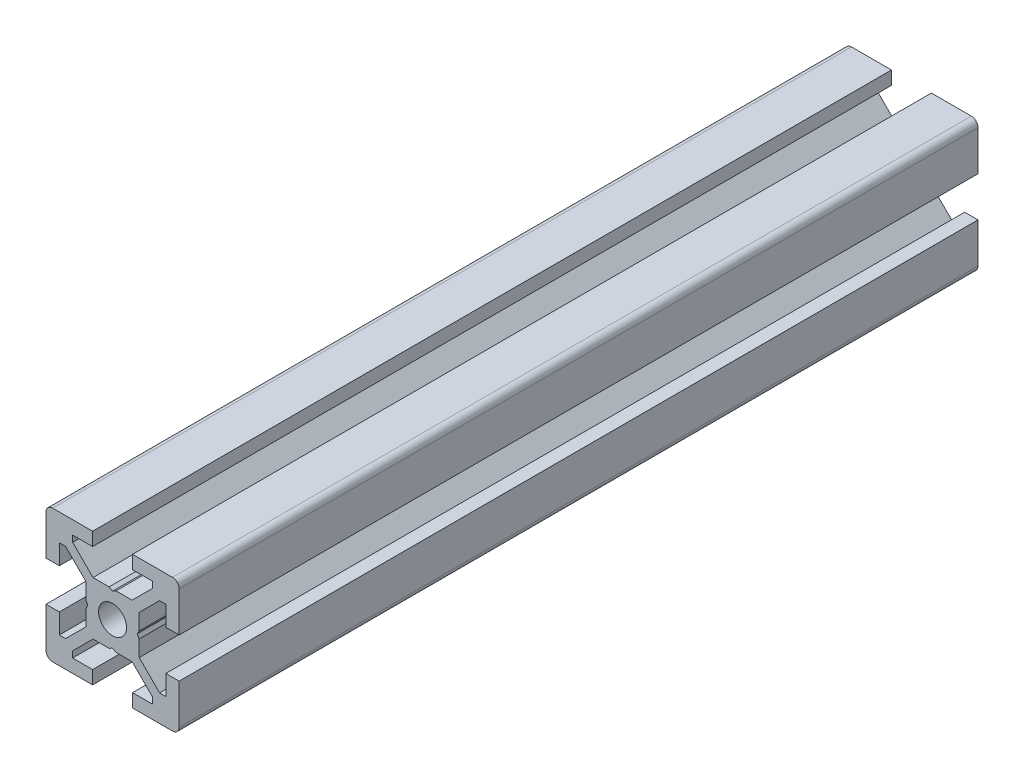
SolidWorks part; units mm, degrees
material "2014 合金"
ref_plane "正面" through (0, 0, 0) normal (0, 0, 1) x (1, 0, 0)
ref_plane "平面" through (0, 0, 0) normal (0, 1, 0) x (1, 0, 0)
ref_plane "右側面" through (0, 0, 0) normal (1, 0, 0) x (0, 0, -1)
ref_plane "平面1" through (0, 0, 0) normal (0, 0, 1) x (1, 0, 0)
sketch "ｽｹｯﾁ1" plane through (0, 0, 0) normal (0, 0, 1) x (1, 0, 0)
  line L0 (-10, -3) -> (-10, -9)
  line L1 (-9, -10) -> (-3, -10)
  line L2 (-3, -10) -> (-3, -8)
  line L3 (-3, -8) -> (-6, -8)
  line L4 (-6, -8) -> (-6, -7.0607)
  line L5 (-6, -7.0607) -> (-2.9393, -4)
  line L6 (-2.9393, -4) -> (-0.5196, -4)
  line L7 (-0.5196, -4) -> (0, -3.7)
  line L8 (0, -3.7) -> (0.5196, -4)
  line L9 (0.5196, -4) -> (2.9393, -4)
  line L10 (2.9393, -4) -> (6, -7.0607)
  line L11 (6, -7.0607) -> (6, -8)
  line L12 (6, -8) -> (3, -8)
  line L13 (3, -8) -> (3, -10)
  line L14 (3, -10) -> (9, -10)
  line L15 (10, -9) -> (10, -3)
  line L16 (10, -3) -> (8, -3)
  line L17 (8, -3) -> (8, -6)
  line L18 (8, -6) -> (7.0607, -6)
  line L19 (7.0607, -6) -> (4, -2.9393)
  line L20 (4, -2.9393) -> (4, -0.5196)
  line L21 (4, -0.5196) -> (3.7, 0)
  line L22 (3.7, 0) -> (4, 0.5196)
  line L23 (4, 0.5196) -> (4, 2.9393)
  line L24 (4, 2.9393) -> (7.0607, 6)
  line L25 (7.0607, 6) -> (8, 6)
  line L26 (8, 6) -> (8, 3)
  line L27 (8, 3) -> (10, 3)
  line L28 (10, 3) -> (10, 9)
  line L29 (9, 10) -> (3, 10)
  line L30 (3, 10) -> (3, 8)
  line L31 (3, 8) -> (6, 8)
  line L32 (6, 8) -> (6, 7.0607)
  line L33 (6, 7.0607) -> (2.9393, 4)
  line L34 (2.9393, 4) -> (0.5196, 4)
  line L35 (0.5196, 4) -> (0, 3.7)
  line L36 (0, 3.7) -> (-0.5196, 4)
  line L37 (-0.5196, 4) -> (-2.9393, 4)
  line L38 (-2.9393, 4) -> (-6, 7.0607)
  line L39 (-6, 7.0607) -> (-6, 8)
  line L40 (-6, 8) -> (-3, 8)
  line L41 (-3, 8) -> (-3, 10)
  line L42 (-3, 10) -> (-9, 10)
  line L43 (-10, 9) -> (-10, 3)
  line L44 (-10, 3) -> (-8, 3)
  line L45 (-8, 3) -> (-8, 6)
  line L46 (-8, 6) -> (-7.0607, 6)
  line L47 (-7.0607, 6) -> (-4, 2.9393)
  line L48 (-4, 2.9393) -> (-4, 0.5196)
  line L49 (-4, 0.5196) -> (-3.7, 0)
  line L50 (-3.7, 0) -> (-4, -0.5196)
  line L51 (-4, -0.5196) -> (-4, -2.9393)
  line L52 (-4, -2.9393) -> (-7.0607, -6)
  line L53 (-7.0607, -6) -> (-8, -6)
  line L54 (-8, -6) -> (-8, -3)
  line L55 (-8, -3) -> (-10, -3)
  arc A0 (-10, -9) -> (-9, -10) centre (-9, -9) ccw
  arc A1 (9, -10) -> (10, -9) centre (9, -9) ccw
  arc A2 (10, 9) -> (9, 10) centre (9, 9) ccw
  arc A3 (-9, 10) -> (-10, 9) centre (-9, 9) ccw
extrude "ﾎﾞｽ - 押し出し1" add sketch "ｽｹｯﾁ1" against normal blind 120
ref_plane "平面2" through (0, 0, 0) normal (1, 0, 0) x (0, 0, -1)
sketch "ｽｹｯﾁ2" plane through (0, 0, 0) normal (1, 0, 0) x (0, 0, -1)
  line L0 (0, 0) -> (0, 2.1)
  line L1 (0, 2.1) -> (260, 2.1)
  line L2 (260, 2.1) -> (260, 0)
  line L3 (260, 0) -> (0, 0)
  line L4 (260, 0) -> (0, 0) construction
revolve "ｶｯﾄ - 回転1" cut sketch "ｽｹｯﾁ2" angle 360 about L4
